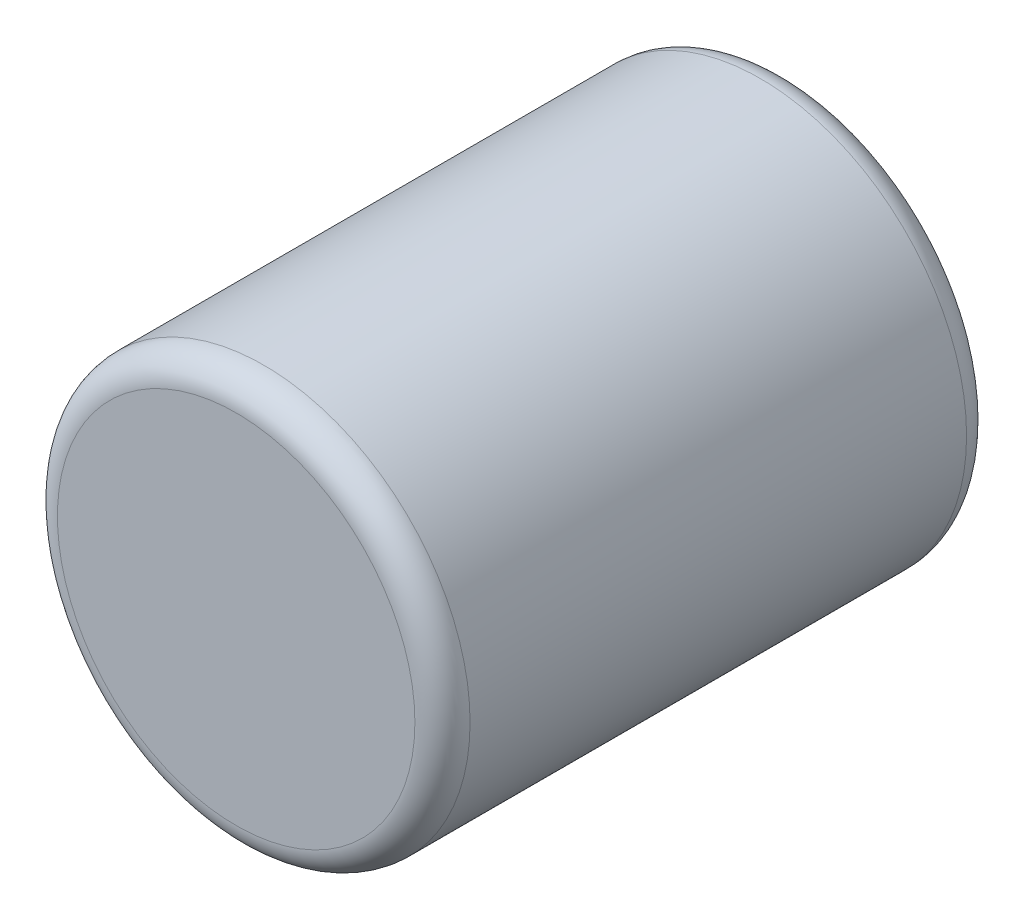
SolidWorks part; units mm, degrees
ref_plane "Front Plane" through (0, 0, 0) normal (0, 0, 1) x (1, 0, 0)
ref_plane "Top Plane" through (0, 0, 0) normal (0, 1, 0) x (1, 0, 0)
ref_plane "Right Plane" through (0, 0, 0) normal (1, 0, 0) x (0, 0, -1)
sketch "Sketch1" plane through (0, 0, 0) normal (0, 0, 1) x (1, 0, 0)
  circle A0 centre (0, 0) radius 47.498
  dimension "D1" = 94.996
extrude "Boss-Extrude1" add sketch "Sketch1" against normal blind 127
fillet "Fillet1" radius 6.35 2 edges at (47.498, 0, -127) (47.498, 0, 0)
